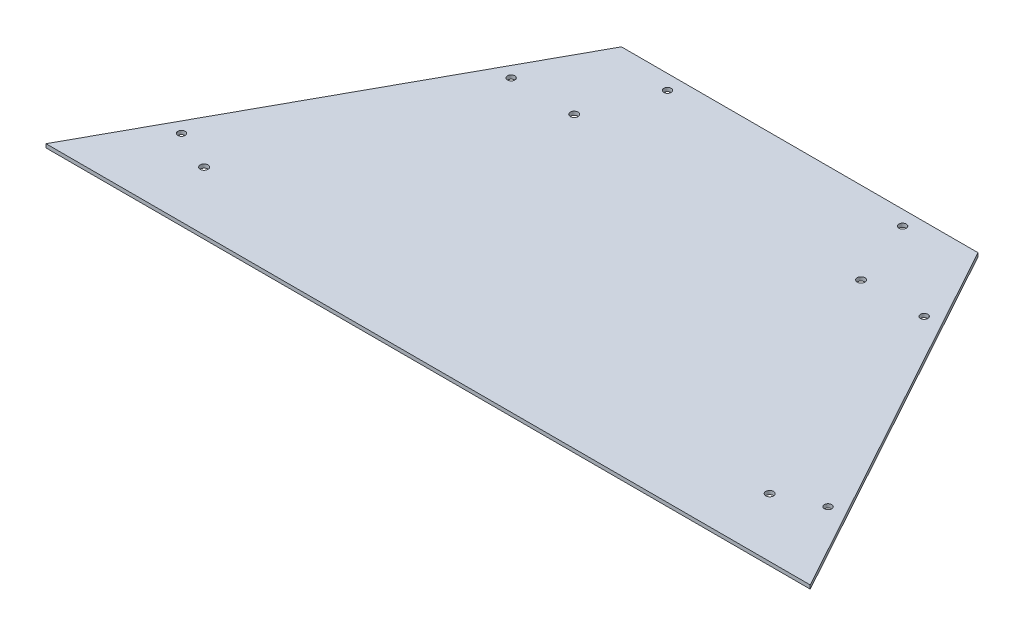
SolidWorks part; units mm, degrees
material "PC High Viscosity"
ref_plane "Front Plane" through (0, 0, 0) normal (0, 0, 1) x (1, 0, 0)
ref_plane "Top Plane" through (0, 0, 0) normal (0, 1, 0) x (1, 0, 0)
ref_plane "Right Plane" through (0, 0, 0) normal (1, 0, 0) x (0, 0, -1)
sketch "Sketch1" plane through (0, 0, 0) normal (0, 1, 0) x (1, 0, 0)
  line L0 (-330.2, 0) -> (-154.051, 321.1289)
  line L1 (-154.051, 321.1289) -> (154.051, 321.1289)
  line L2 (154.051, 321.1289) -> (330.2, 0)
  line L3 (330.2, 0) -> (-330.2, 0)
  point P4 (0, 0)
  dimension "D1" = 660.4
  dimension "D2" = 366.268
  dimension "D3" = 308.102
extrude "Boss-Extrude1" add sketch "Sketch1" along normal blind 3.175
hole_wizard "1/4 (0.25) Diameter Hole1" positions "Sketch2" profile "Sketch3" hole size "1/4" standard "ANSI Inch" end condition through all
sketch "Sketch2" plane through (0, 3.175, 0) normal (0, 1, 0) x (1, 0, 0)
  line L0 (-101.6, 308.4289) -> (-101.6, 321.1289)
  line L1 (154.051, 321.1289) -> (-154.051, 321.1289) construction
  line L3 (-178.4636, 250.2163) -> (-189.5984, 256.3241)
  line L4 (-154.051, 321.1289) -> (-330.2, 0) construction
  line L6 (-279.3644, 66.2687) -> (-290.4993, 72.3765)
  line L8 (0, 0) -> (0, 321.1289) construction
  point P0 (-279.3644, 66.2687)
  point P2 (-178.4636, 250.2163)
  point P4 (-101.6, 308.4289)
  point P28 (279.3644, 66.2687)
  point P29 (178.4636, 250.2163)
  point P30 (101.6, 308.4289)
  dimension "D1" = 12.7
  dimension "D2" = 82.55
  dimension "D3" = 292.354
  dimension "D4" = 101.6
sketch "Sketch3" plane through (-279.3644, 3.175, -66.2687) normal (1, 0, 0) x (0, 0, 1)
  line L0 (0, 0) -> (0, 3.175)
  line L1 (0, 3.175) -> (3.175, 3.175)
  line L2 (3.175, 3.175) -> (3.175, 0)
  line L5 (3.175, 0) -> (0, 0)
  line L11 (0, -6.35) -> (0, 107.95) construction
  dimension "Thru Hole Dia." = 6.35
  dimension "Thru Hole Depth" = 3.175
hole_wizard "1/4 Clearance Hole1" positions "Sketch4" profile "Sketch5" hole size "1/4" standard "ANSI Inch" end condition through all
sketch "Sketch4" plane through (0, 3.175, 0) normal (0, 1, 0) x (1, 0, 0)
  line L0 (0, 0) -> (0, 321.1289) construction
  line L1 (154.051, 321.1289) -> (-154.051, 321.1289) construction
  line L3 (-330.2, 0) -> (330.2, 0) construction
  line L4 (178.4636, 250.2163) -> (-178.4636, 250.2163) construction
  point P0 (-123.952, 250.2163)
  point P2 (-244.348, 50.8)
  point P13 (244.348, 50.8)
  point P14 (123.952, 250.2163)
  point P24 (0, 0)
  dimension "D1" = 50.8
  dimension "D2" = 244.348
  dimension "D3" = 123.952
  dimension "D4" = 250.2163
sketch "Sketch5" plane through (-123.952, 3.175, -250.2163) normal (1, 0, 0) x (0, 0, 1)
  line L0 (0, 0) -> (0, 3.175)
  line L1 (0, 3.175) -> (3.3782, 3.175)
  line L2 (3.3782, 3.175) -> (3.3782, 0)
  line L5 (3.3782, 0) -> (0, 0)
  line L11 (0, -6.35) -> (0, 107.95) construction
  dimension "Thru Hole Dia." = 6.7564
  dimension "Thru Hole Depth" = 3.175
